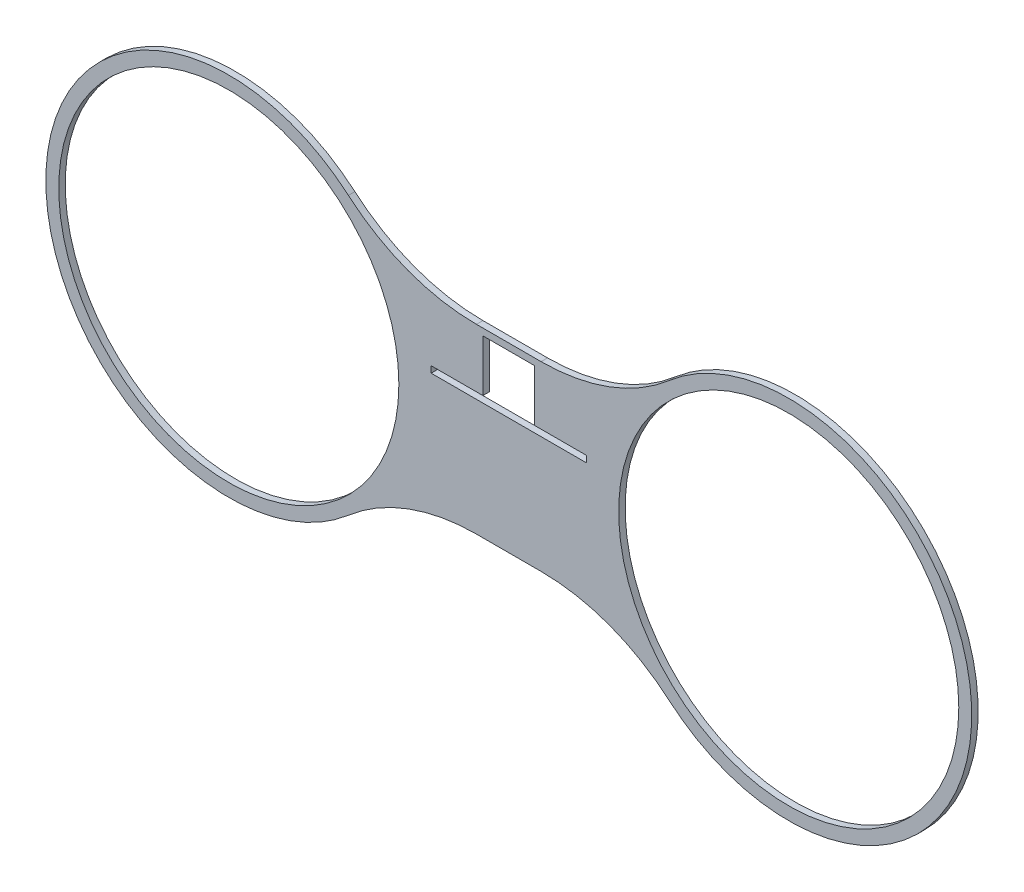
SolidWorks part; units mm, degrees
ref_plane "Front Plane" through (0, 0, 0) normal (0, 0, 1) x (1, 0, 0)
ref_plane "Top Plane" through (0, 0, 0) normal (0, 1, 0) x (1, 0, 0)
ref_plane "Right Plane" through (0, 0, 0) normal (1, 0, 0) x (0, 0, -1)
sketch "Sketch1" plane through (0, 0, 0) normal (0, 0, 1) x (1, 0, 0)
  line L0 (137.419, 0) -> (-137.4211, 0) construction
  line L1 (-15.8547, -44.5943) -> (15.8526, -44.5943)
  line L2 (15.8526, 44.5943) -> (-15.8547, 44.5943)
  line L3 (-0.0011, 44.5943) -> (-0.0011, -44.5943) construction
  line L4 (-78.704, 67.9795) -> (78.7018, -67.9795) construction
  line L5 (-78.704, -67.9795) -> (78.7018, 67.9795) construction
  circle A0 centre (137.419, 0) radius 83.4771 construction
  circle A1 centre (-137.4211, 0) radius 83.4771 construction
  circle A2 centre (137.419, 0) radius 83.4771
  circle A3 centre (-137.4211, 0) radius 83.4771
  arc A4 (-78.704, -67.9795) -> (-78.704, 67.9795) centre (-137.4211, 0) cw
  arc A5 (78.7018, -67.9795) -> (78.7018, 67.9795) centre (137.419, 0) ccw
  arc A6 (-78.704, 67.9795) -> (-15.8547, 44.5943) centre (-15.8547, 140.7429) ccw
  arc A7 (78.7018, 67.9795) -> (15.8526, 44.5943) centre (15.8526, 140.7429) cw
  arc A8 (78.7018, -67.9795) -> (15.8526, -44.5943) centre (15.8526, -140.7429) ccw
  arc A9 (-78.704, -67.9795) -> (-15.8547, -44.5943) centre (-15.8547, -140.7429) cw
  circle A11 centre (0, 28.575) radius 3.175
  point P10 (0, 0)
  point P16 (-0.0011, 44.5943)
  point P19 (-0.0011, 0)
  point P25 (-0.0011, 0)
  dimension "D1" = 16.0193
  dimension "D2" = 6.35
  dimension "D4" = 6.35
  dimension "D5" = 89.1887
extrude "Boss-Extrude1" add sketch "Sketch1" along normal blind 3.175
sketch "Sketch2" plane through (0, 0, 3.175) normal (0, 0, 1) x (1, 0, 0)
  line L1 (-12.7, 41.275) -> (12.7, 41.275)
  line L2 (-12.7, 41.275) -> (-12.7, 15.875)
  line L3 (-12.7, 15.875) -> (12.7, 15.875)
  line L4 (12.7, 41.275) -> (12.7, 15.875)
  line L5 (-12.7, 41.275) -> (12.7, 15.875) construction
  line L6 (-12.7, 15.875) -> (12.7, 41.275) construction
  point P0 (0, 28.575)
  dimension "D1" = 25.4
  dimension "D2" = 25.4
extrude "Cut-Extrude1" cut sketch "Sketch2" against normal through all
sketch "Sketch3" plane through (0, 0, 3.175) normal (0, 0, 1) x (1, 0, 0)
  line L0 (-38.1, 12.7) -> (-38.1, 15.875)
  line L1 (-38.1, 12.7) -> (38.1, 12.7)
  line L2 (-38.1, 15.875) -> (38.1, 15.875)
  line L3 (38.1, 12.7) -> (38.1, 15.875)
  line L4 (-38.1, 12.7) -> (38.1, 15.875) construction
  line L5 (-38.1, 15.875) -> (38.1, 12.7) construction
  line L6 (12.7, 41.275) -> (-12.7, 41.275) construction
  line L7 (-12.7, 15.875) -> (12.7, 15.875) construction
  point P1 (0, 14.2875)
  point P3 (0, 41.275)
  point P4 (0, 11.042)
  dimension "D1" = 76.2
  dimension "D2" = 3.175
extrude "Cut-Extrude2" cut sketch "Sketch3" against normal through all
